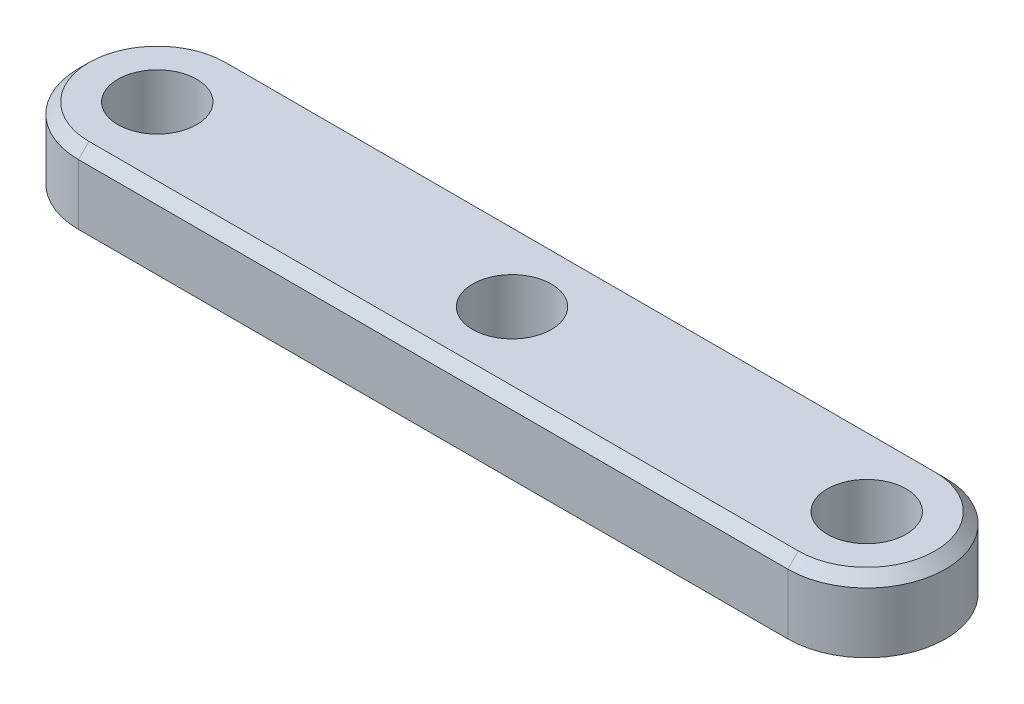
SolidWorks part; units mm, degrees
ref_plane "Front Plane" through (0, 0, 0) normal (0, 0, 1) x (1, 0, 0)
ref_plane "Top Plane" through (0, 0, 0) normal (0, 1, 0) x (1, 0, 0)
ref_plane "Right Plane" through (0, 0, 0) normal (1, 0, 0) x (0, 0, -1)
sketch "Sketch1" plane through (0, 0, 0) normal (0, 1, 0) x (1, 0, 0)
  line L0 (-18.0944, 0) -> (24.4801, 0) construction
  line L1 (-13.5, 0) -> (13.5, 0) construction
  line L2 (-13.5, 3) -> (13.5, 3)
  line L3 (-13.5, -3) -> (13.5, -3)
  line L4 (0, 10.1131) -> (0, -14.786) construction
  arc A0 (-13.5, 3) -> (-13.5, -3) centre (-13.5, 0) ccw
  arc A1 (13.5, -3) -> (13.5, 3) centre (13.5, 0) ccw
  circle A2 centre (-13.5, 0) radius 1.5
  circle A4 centre (13.5, 0) radius 1.5
  circle A5 centre (0, 0) radius 1.5
  point P5 (0, 0)
  point P11 (-16.5, 0)
  point P12 (16.5, 0)
  dimension "D3" = 3
  dimension "D4" = 3
  dimension "D1" = 6
  dimension "D2" = 33
extrude "Boss-Extrude1" add sketch "Sketch1" along normal mid plane 2.7
chamfer "Chamfer1" distance 0.4 angle 45 4 edges at (16.5, 1.35, 0) (0, 1.35, -3) (-16.5, 1.35, 0) (0, 1.35, 3)
